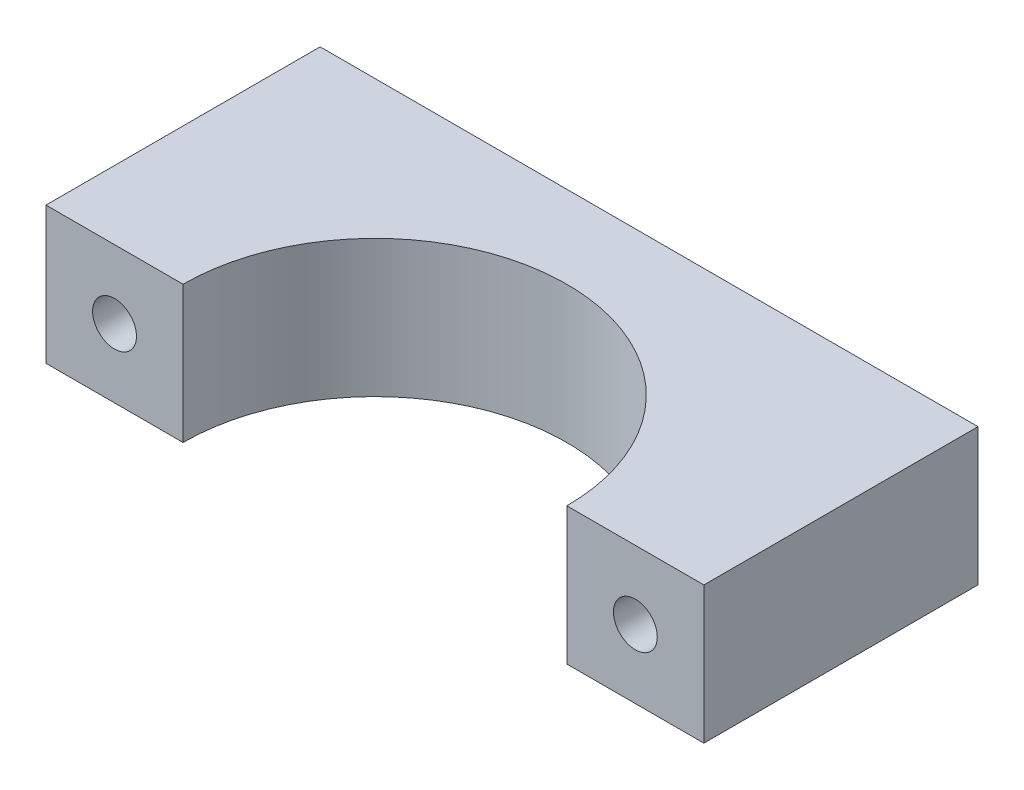
SolidWorks part; units mm, degrees
ref_plane "Ebene vorne" through (0, 0, 0) normal (0, 0, 1) x (1, 0, 0)
ref_plane "Ebene oben" through (0, 0, 0) normal (0, 1, 0) x (1, 0, 0)
ref_plane "Ebene rechts" through (0, 0, 0) normal (1, 0, 0) x (0, 0, -1)
sketch "Skizze1" plane through (0, 0, 0) normal (0, 1, 0) x (1, 0, 0)
  line L0 (14, -1) -> (24, -1)
  line L1 (24, -1) -> (24, 19)
  line L2 (24, 19) -> (-24, 19)
  line L3 (-24, 19) -> (-24, -1)
  line L4 (-24, -1) -> (-14, -1)
  arc A0 (-14, -1) -> (14, -1) centre (0, -1) cw
  dimension "D1" = 14
  dimension "D2" = 1
  dimension "D3" = 10
  dimension "D4" = 20
extrude "Aufsatz-Linear austragen1" add sketch "Skizze1" along normal blind 10
sketch "Skizze2" plane through (0, 0, 1) normal (0, 0, 1) x (1, 0, 0)
  line L0 (-24, 10) -> (-14, 0) construction
  line L1 (24, 10) -> (14, 0) construction
  circle A0 centre (-19, 5) radius 1.6
  circle A1 centre (19, 5) radius 1.6
  dimension "D1" = 3.2
extrude "Schnitt-Linear austragen1" cut sketch "Skizze2" against normal through all
sketch "Skizze3" plane through (0, 0, -19) normal (0, 0, -1) x (-1, 0, 0)
  circle A0 centre (-19, 5) radius 3
  circle A1 centre (19, 5) radius 3
  dimension "D1" = 6
extrude "Schnitt-Linear austragen2" cut sketch "Skizze3" against normal blind 13
